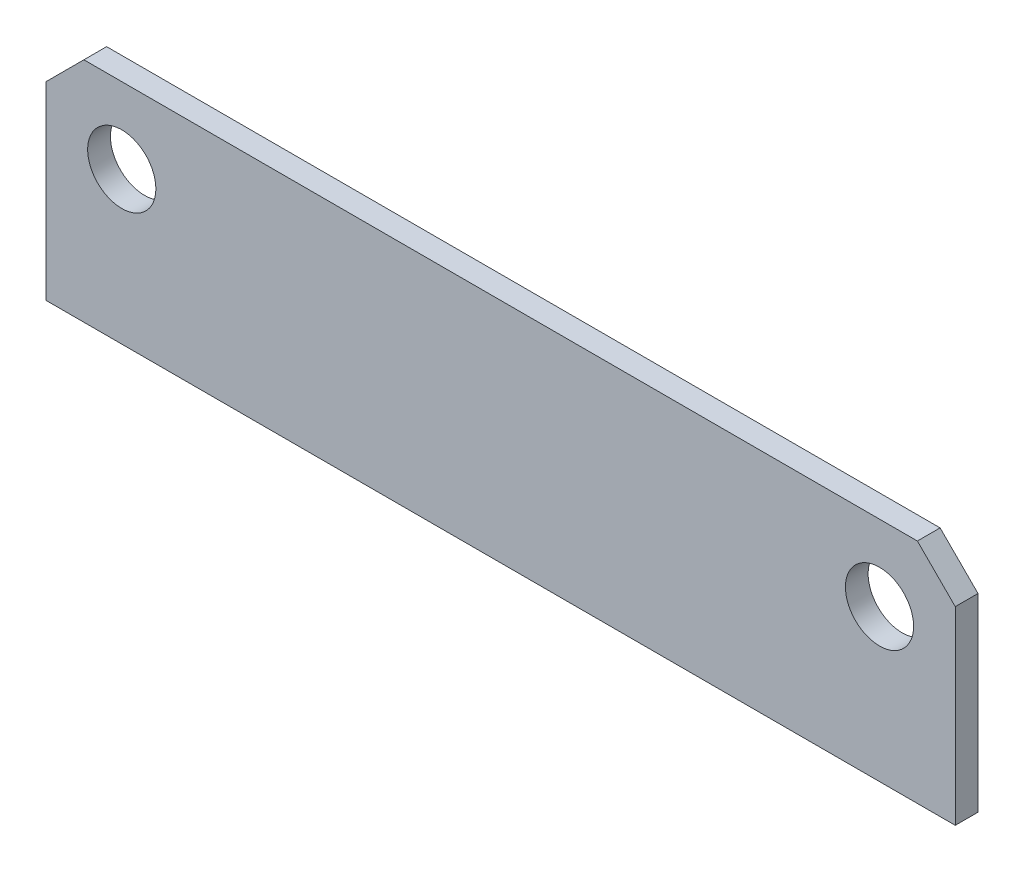
SolidWorks part; units mm, degrees
ref_plane "Alzado" through (0, 0, 0) normal (0, 0, 1) x (1, 0, 0)
ref_plane "Planta" through (0, 0, 0) normal (0, 1, 0) x (1, 0, 0)
ref_plane "Vista lateral" through (0, 0, 0) normal (1, 0, 0) x (0, 0, -1)
sketch "Croquis1" plane through (0, 0, 0) normal (0, 0, 1) x (1, 0, 0)
  line L0 (-60, 25) -> (-55, 30)
  line L1 (-55, 30) -> (55, 30)
  line L2 (-60, 25) -> (-60, 0)
  line L3 (-60, 0) -> (60, 0)
  line L4 (60, 25) -> (60, 0)
  line L5 (55, 30) -> (60, 25)
  circle A0 centre (-50, 20) radius 4.5
  circle A1 centre (50, 20) radius 4.5
  point P0 (-60, 30)
  point P3 (60, 30)
  dimension "D4" = 9
  dimension "D1" = 120
  dimension "D2" = 30
  dimension "D3" = 60
  dimension "D5" = 10
  dimension "D6" = 100
  dimension "D7" = 50
extrude "Saliente-Extruir1" add sketch "Croquis1" along normal blind 3
